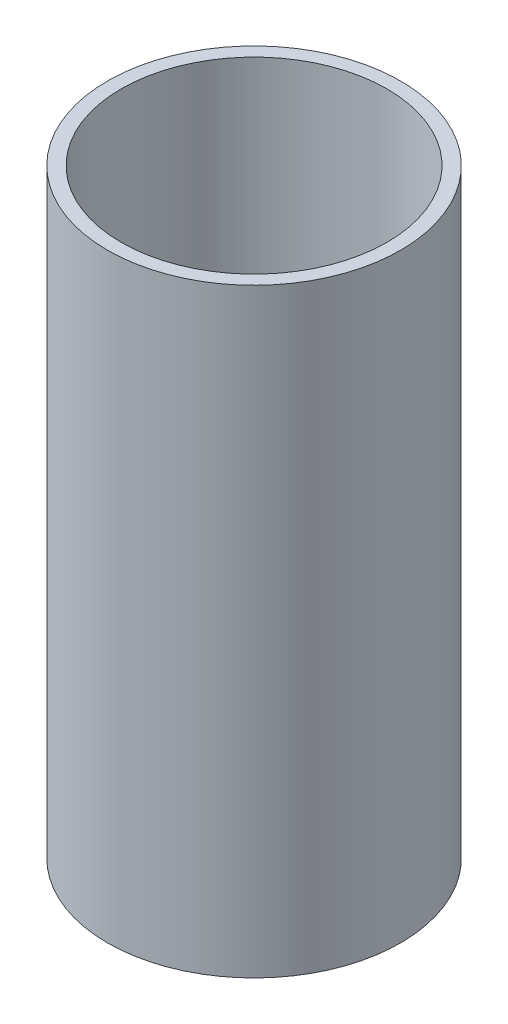
SolidWorks part; units mm, degrees
ref_plane "Front Plane" through (0, 0, 0) normal (0, 0, 1) x (1, 0, 0)
ref_plane "Top Plane" through (0, 0, 0) normal (0, 1, 0) x (1, 0, 0)
ref_plane "Right Plane" through (0, 0, 0) normal (1, 0, 0) x (0, 0, -1)
sketch "Sketch1" plane through (0, 0, 0) normal (0, 1, 0) x (1, 0, 0)
  line L0 (0, 0) -> (0, 50000) construction
  line L1 (0, 0) -> (50000, 0) construction
  circle A0 centre (0, 0) radius 9.75
  circle A1 centre (0, 0) radius 10.75
  dimension "D1" = 19.5
  dimension "D2" = 1
extrude "Boss-Extrude1" add sketch "Sketch1" along normal blind 44
fillet "Fillet2" [suppressed] radius 0.4
sketch "Sketch2" [suppressed] plane through (0, 0, 0) normal (1, 0, 0) x (0, 0, -1)
  line L0 (-18.6797, 39) -> (49981.3203, 39) construction
  line L1 (-17.4508, 15) -> (49982.5492, 15) construction
  line L2 (9.15, 44) -> (-9.15, 44) construction
  line L3 (-9.75, 0) -> (9.75, 0) construction
  line L4 (-2, 39) -> (-2, 15)
  line L5 (0, 0) -> (0, 50000) construction
  line L6 (-2, 15) -> (2, 15)
  line L7 (-2, 39) -> (2, 39)
  line L8 (2, 39) -> (2, 15)
  point P12 (0, 0)
  point P17 (0, 39)
  point P18 (0, 15)
  dimension "D1" = 5
  dimension "D2" = 15
  dimension "D3" = 2
extrude "Cut-Extrude1" [suppressed] cut sketch "Sketch2" against normal through all and the other way through all
chamfer "Chamfer1" [suppressed] distance 2 angle 45
